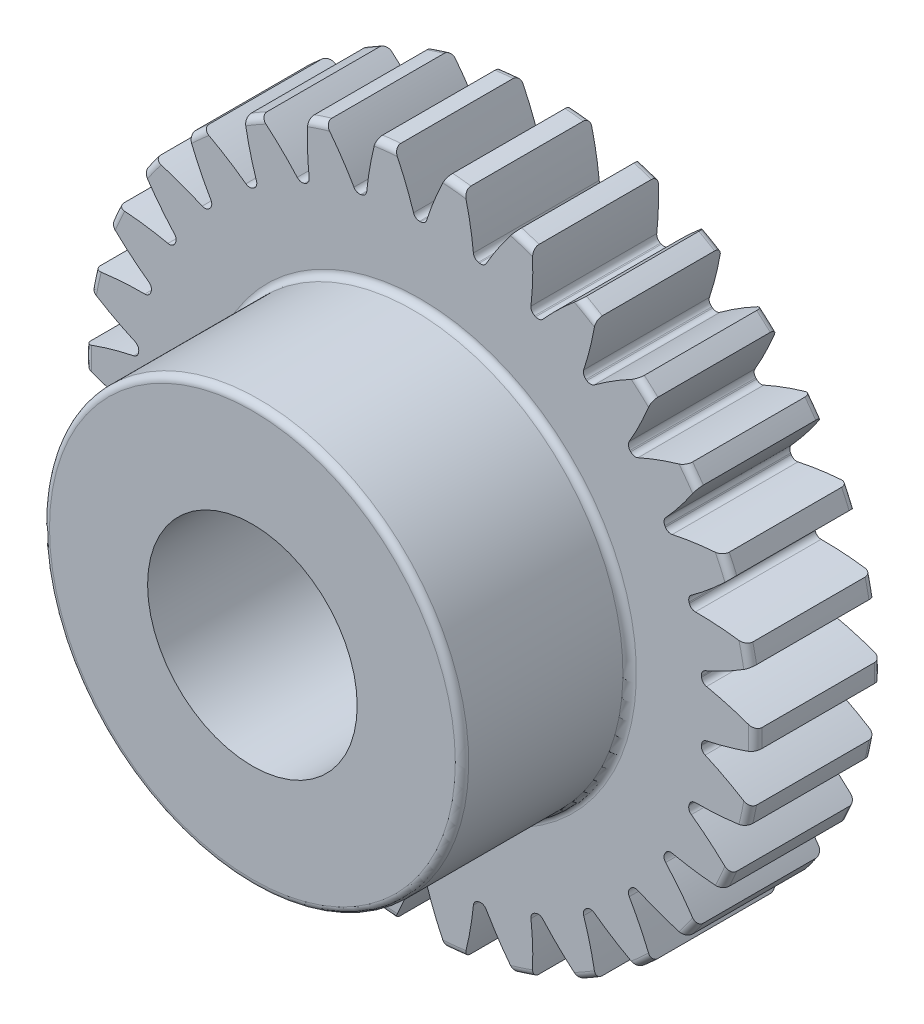
SolidWorks part; units mm, degrees
ref_plane "Front Plane" through (0, 0, 0) normal (0, 0, 1) x (1, 0, 0)
ref_plane "Top Plane" through (0, 0, 0) normal (0, 1, 0) x (1, 0, 0)
ref_plane "Right Plane" through (0, 0, 0) normal (1, 0, 0) x (0, 0, -1)
sketch "Sketch1" plane through (0, 0, 0) normal (0, 0, 1) x (1, 0, 0)
  line L0 (-381, 0) -> (381, 0) construction
  circle A0 centre (0, 0) radius 8 construction
  circle A1 centre (0, 0) radius 7.5 construction
  circle A2 centre (0, 0) radius 6.75 construction
  circle A3 centre (0, 0) radius 5 construction
  circle A4 centre (0, 0) radius 2.5 construction
  dimension "D2" = 0.5
  dimension "D3" = 1.25
  dimension "D1" = 1.25
sketch "Sketch2" plane through (0, 0, 0) normal (1, 0, 0) x (0, 0, -1)
  line L0 (0, 0) -> (-3, 0) construction
  line L1 (-3, 0) -> (-7, 0) construction
  dimension "Overall Width" = 7
  dimension "Face Width" = 3
sketch "Sketch4" plane through (0, 0, 0) normal (1, 0, 0) x (0, 0, -1)
  line L0 (-7, 2.5) -> (-7, 5)
  line L1 (-7, 5) -> (-3, 5)
  line L2 (-3, 5) -> (-3, 8)
  line L3 (-3, 8) -> (0, 8)
  line L4 (0, 8) -> (0, 2.5)
  line L5 (-3, 5) -> (-3, 0) construction
  line L6 (0, 8) -> (0, -8) construction
  line L7 (-3, 5) -> (0, 5) construction
  line L12 (-7, 2.5) -> (0, 2.5)
revolve "Revolve1" add sketch "Sketch4" angle 360 about L1
fillet "Fillet2" radius 0.16 4 edges at (0, 5, 7) (0, 5, 3) (0, 8, 3) (0, 8, 0)
sketch "Sketch7" plane through (0, 0, 3) normal (0, 0, 1) x (1, 0, 0)
  line L0 (0, 0) -> (0, 8) construction
  line L1 (0.3925, 7.4897) -> (0.5996, 7.9775) construction
  line L3 (0.8362, 7.9562) -> (0.784, 7.4589) construction
  line L4 (0.784, 7.4589) -> (0.7056, 6.713) construction
  line L5 (0, 0) -> (0.7056, 6.713) construction
  line L6 (0.3925, 7.4897) -> (0, 0) construction
  line L7 (0.3925, 7.4897) -> (0.4187, 7.989) construction
  line L8 (0.3925, 7.4897) -> (0, 0) construction
  circle A0 centre (0, 0) radius 8 construction
  arc A1 (-0.0129, 6.75) -> (0.0129, 6.75) centre (0, 0) cw
  circle A2 centre (0, 0) radius 6.75 construction
  arc A3 (-0.3925, 7.4897) -> (0.3925, 7.4897) centre (0, 0) cw construction
  circle A4 centre (0, 0) radius 7.5 construction
  arc A5 (1.0521, 7.9305) -> (0.6198, 7.976) centre (0, 0) ccw construction
  arc A6 (0.3925, 7.4897) -> (1.1733, 7.4077) centre (0, 0) cw construction
  arc A7 (-0.6198, 7.976) -> (0.6198, 7.976) centre (0, 0) cw
  arc A8 (0.156, 6.8541) -> (0.6198, 7.976) centre (7.2963, 4.5592) cw
  arc A9 (-0.156, 6.8541) -> (-0.6198, 7.976) centre (-7.2963, 4.5592) ccw
  arc A10 (-0.0129, 6.75) -> (-0.156, 6.8541) centre (-0.0132, 6.9) cw
  arc A11 (0.0129, 6.75) -> (0.156, 6.8541) centre (0.0132, 6.9) ccw
  point P26 (-0.1231, 6.7489)
  point P29 (0.1231, 6.7489)
  dimension "D4" = 0.15
  dimension "D5" = 7.5
  dimension "D3" = 20
  dimension "D1" = 1.5708
  dimension "D2" = 0.7854
extrude "Cut-Extrude2" cut sketch "Sketch7" against normal through all
pattern_circular "CirPattern1" count 30 over 360 about axis through (0, 0, 0) along (0, 0, 1) of "Cut-Extrude2"
equation "\"D1@Sketch1\"=2.5*(\"Pitch Dia.@Sketch1\"/\"Number of Teeth@Sketch1\")"
equation "\"D1@CirPattern1\"=\"Number of Teeth@Sketch1\""
equation "\"D1@Fillet2\"=\"OD@Sketch1\"*.01"
equation "\"D1@Sketch7\"=3.14159*(\"Pitch Dia.@Sketch1\"/\"Number of Teeth@Sketch1\")"
equation "\"D2@Sketch7\"=\"D1@Sketch7\"/2"
equation "\"D4@Sketch7\"=\"D1@Sketch7\"*.0955"
equation "\"D5@Sketch7\"=\"Pitch Dia.@Sketch1\"/2"
